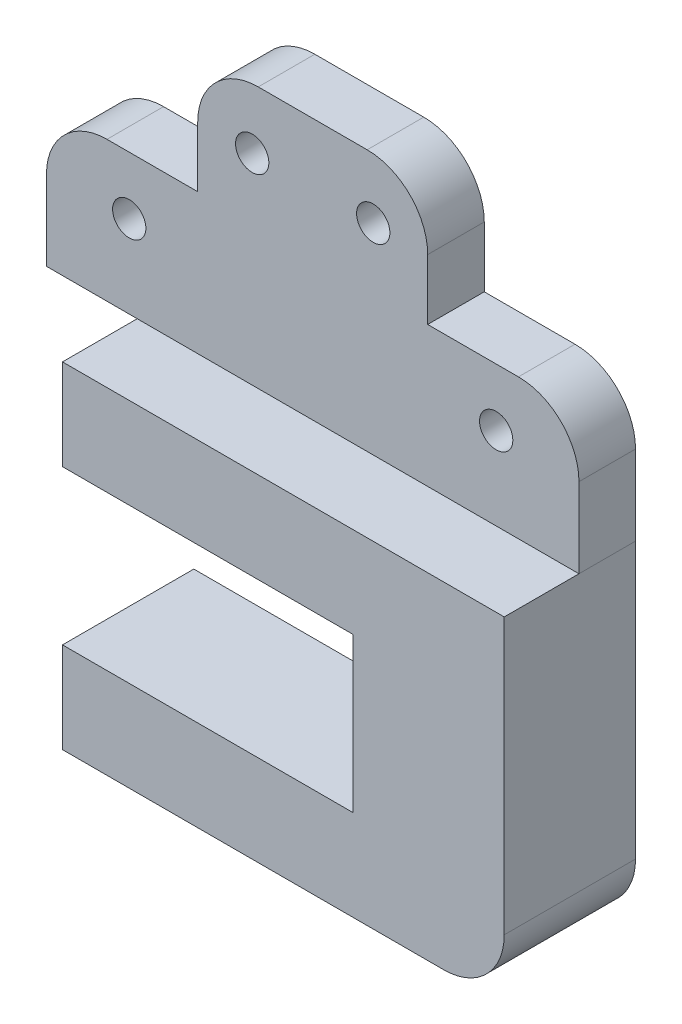
SolidWorks part; units mm, degrees
material "PETG"
ref_plane "Front Plane" through (0, 0, 0) normal (0, 0, 1) x (1, 0, 0)
ref_plane "Top Plane" through (0, 0, 0) normal (0, 1, 0) x (1, 0, 0)
ref_plane "Right Plane" through (0, 0, 0) normal (1, 0, 0) x (0, 0, -1)
sketch "Sketch1" plane through (0, 0, 0) normal (0, 0, 1) x (1, 0, 0)
  line L0 (-44, 0) -> (-44, 23.18)
  line L1 (-44, 23.18) -> (-19, 23.18)
  line L2 (-19, 23.18) -> (-19, 43.18)
  line L3 (-19, 43.18) -> (19, 43.18)
  line L4 (-44, 0) -> (44, 0)
  line L5 (0, 43.18) -> (0, -1.1735) construction
  line L6 (44, 0) -> (44, 23.18)
  line L7 (44, 23.18) -> (19, 23.18)
  line L8 (19, 23.18) -> (19, 43.18)
  circle A0 centre (10, 33.18) radius 2.75
  circle A1 centre (30.32, 13.65) radius 2.75
  circle A2 centre (-30.32, 13.65) radius 2.75
  circle A3 centre (-10, 33.18) radius 2.75
  point P9 (0, 0)
  dimension "D4" = 5.5
  dimension "D5" = 19.53
  dimension "D6" = 20.32
  dimension "D7" = 13.68
  dimension "D8" = 13.65
  dimension "D1" = 88
  dimension "D2" = 20
  dimension "D3" = 25
  dimension "D9" = 10
extrude "Boss-Extrude1" add sketch "Sketch1" along normal blind 9.35
sketch "Sketch2" plane through (0, 0, 0) normal (0, 0, -1) x (-1, 0, 0)
  line L0 (-44, 0) -> (-44, -55.5)
  line L1 (-44, -55.5) -> (29, -55.5)
  line L2 (29, -55.5) -> (29, -40.5)
  line L3 (29, -40.5) -> (-19, -40.5)
  line L4 (-19, -40.5) -> (-19, -15)
  line L5 (-19, -15) -> (29, -15)
  line L6 (-44, 0) -> (29, 0)
  line L7 (44, 23.18) -> (44, 0) construction
  line L8 (29, -15) -> (29, 0)
  line L9 (44, 0) -> (-44, 0) construction
  dimension "D1" = 55.5
  dimension "D2" = 15
  dimension "D3" = 73
  dimension "D4" = 15
  dimension "D5" = 25.5
  dimension "D6" = 48
extrude "Boss-Extrude2" add sketch "Sketch2" against normal blind 21.7 separate body
sketch "Sketch3" plane through (-29, 0, 0) normal (-1, 0, 0) x (0, 0, 1)
  line L0 (5.145, 0) -> (5.145, -15) construction
  line L1 (9.35, 0) -> (0, 0) construction
  line L2 (21.7, -15) -> (0, -15) construction
  line L3 (5.145, -7.5) -> (0, -7.5) construction
  line L5 (0, -15) -> (0, 0) construction
  line L6 (16.555, -7.5) -> (21.7, -7.5) construction
  line L7 (21.7, -15) -> (21.7, 0) construction
  line L8 (10.85, -15) -> (10.85, -40.5) construction
  line L11 (21.7, -15) -> (0, -15) construction
  line L12 (21.7, -40.5) -> (0, -40.5) construction
  line L13 (0, -27.75) -> (21.7, -27.75) construction
  line L14 (0, -40.5) -> (0, -15) construction
  line L15 (21.7, -40.5) -> (21.7, -15) construction
  circle A0 centre (5.145, -7.5) radius 1.75
  circle A1 centre (16.555, -7.5) radius 1.75
  circle A2 centre (5.145, -48) radius 1.75
  circle A3 centre (16.555, -48) radius 1.75
  dimension "D1" = 3.5
  dimension "D2" = 11.41
extrude "Cut-Extrude2" cut sketch "Sketch3" against normal blind 15
fillet "Fillet1" radius 10 4 edges at (44, 23.18, 4.675) (19, 43.18, 4.675) (-19, 43.18, 4.675) (-44, 23.18, 4.675)
fillet "Fillet2" radius 10 1 edges at (44, -55.5, 10.85)
